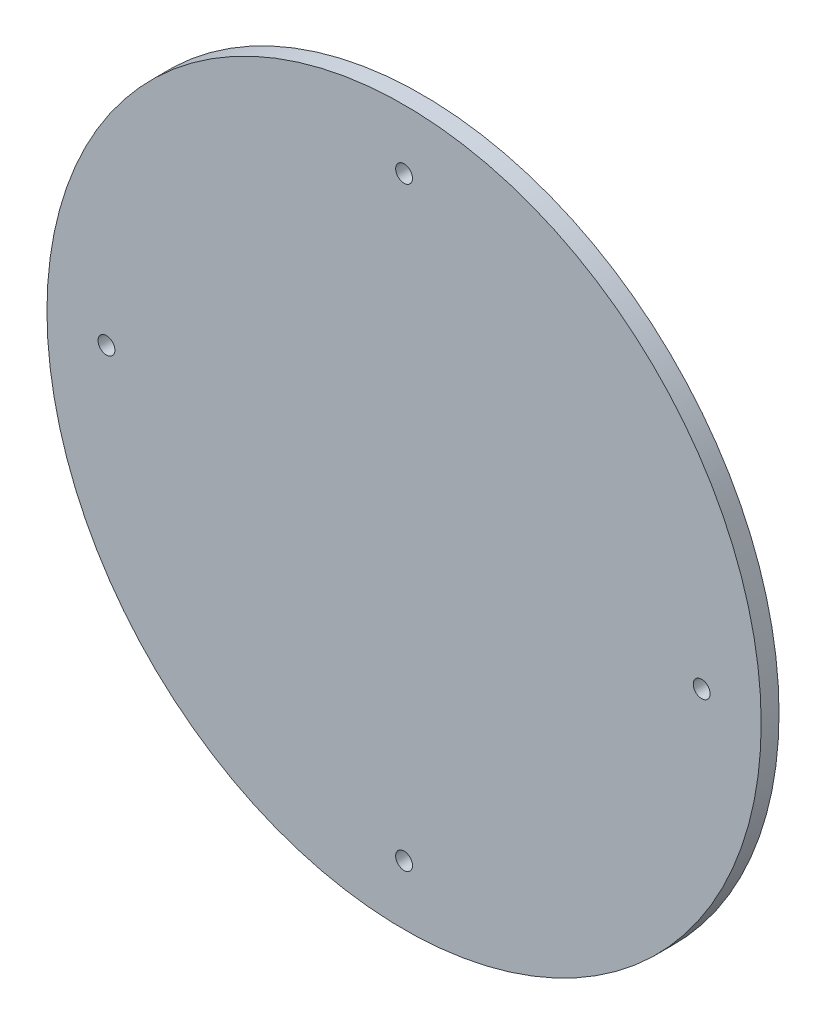
SolidWorks part; units mm, degrees
material "Epoxy, Unfilled"
ref_plane "Front Plane" through (0, 0, 0) normal (0, 0, 1) x (1, 0, 0)
ref_plane "Top Plane" through (0, 0, 0) normal (0, 1, 0) x (1, 0, 0)
ref_plane "Right Plane" through (0, 0, 0) normal (1, 0, 0) x (0, 0, -1)
sketch "Sketch1" plane through (0, 0, 0) normal (0, 0, 1) x (1, 0, 0)
  circle A0 centre (0, 0) radius 95.25
  dimension "D1" = 190.5
extrude "Boss-Extrude1" add sketch "Sketch1" along normal blind 4.7625
hole_wizard "#12-24 Tapped Hole1" positions "Sketch4" profile "Sketch3" tap size "#12-24" standard "ANSI Inch"
sketch "Sketch4" plane through (0, 0, 4.7625) normal (0, 0, 1) x (1, 0, 0)
  circle A0 centre (0, 0) radius 79.375 construction
  point P0 (0, 79.375)
  point P2 (-79.375, 0)
  point P17 (79.375, 0)
  point P18 (0, -79.375)
  dimension "D1" = 158.75
sketch "Sketch3" plane through (0, 79.375, 4.7625) normal (1, 0, 0) x (0, -1, 0)
  line L0 (0, 0) -> (0, 14.224)
  line L1 (0, 14.224) -> (2.2479, 14.224)
  line L2 (2.2479, 14.224) -> (2.2479, 0)
  line L5 (2.2479, 0) -> (0, 0)
  line L10 (0, 14.224) -> (-2.2479, 14.224) construction
  line L11 (0, -6.35) -> (0, 107.95) construction
  dimension "Tap Drill Dia." = 4.4958
  dimension "Tap Drill Depth" = 14.224
  dimension "Drill Angle" = 180
cosmetic thread "Hole Thread1" parameters "D1"=4.7625, "D2"=5.4864
cosmetic thread "Hole Thread2" parameters "D1"=4.7625, "D2"=5.4864
cosmetic thread "Hole Thread3" parameters "D1"=4.7625, "D2"=5.4864
cosmetic thread "Hole Thread4" parameters "D1"=4.7625, "D2"=5.4864
